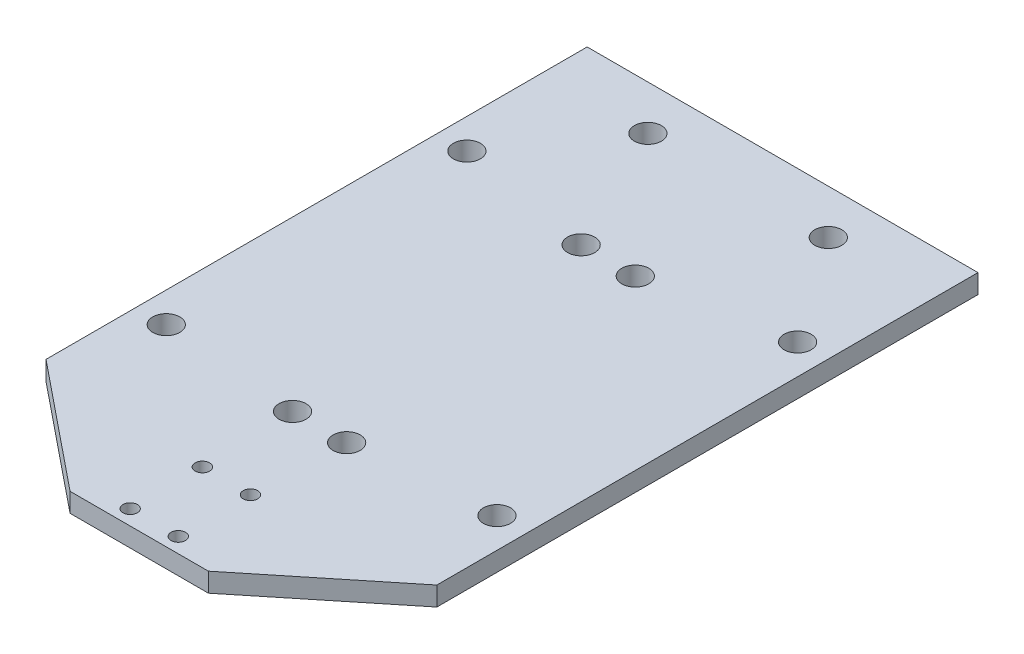
SolidWorks part; units mm, degrees
material "6061-T6 (SS)"
ref_plane "Front Plane" through (0, 0, 0) normal (0, 0, 1) x (1, 0, 0)
ref_plane "Top Plane" through (0, 0, 0) normal (0, 1, 0) x (1, 0, 0)
ref_plane "Right Plane" through (0, 0, 0) normal (1, 0, 0) x (0, 0, -1)
sketch "Sketch1" plane through (0, 0, 0) normal (0, 1, 0) x (1, 0, 0)
  line L0 (-11.5, -62) -> (-32.5, -45)
  line L1 (32.5, -45) -> (-32.5, -45)
  line L2 (32.5, -45) -> (32.5, 45)
  line L3 (32.5, 45) -> (-32.5, 45)
  line L4 (-32.5, -45) -> (-32.5, 45)
  line L5 (32.5, -45) -> (-32.5, 45) construction
  line L6 (32.5, 45) -> (-32.5, -45) construction
  line L7 (-11.5, -45) -> (11.5, -45)
  line L8 (-11.5, -45) -> (-11.5, -62)
  line L9 (-11.5, -62) -> (11.5, -62)
  line L10 (11.5, -45) -> (11.5, -62)
  line L11 (11.5, -62) -> (32.5, -45)
  line L12 (-32.5, -45) -> (32.5, -45)
  line L13 (11.5, -62) -> (-11.5, -62)
  point P0 (0, 0)
  point P10 (0, -62)
  dimension "D1" = 90
  dimension "D2" = 65
  dimension "D3" = 23
  dimension "D4" = 17
  dimension "D5" = 32.5
extrude "Boss-Extrude1" add sketch "Sketch1" along normal mid plane 3.175 contours L8 L1 L0 | L10 L11 L1 | L4 L1 L2 L3 | L10 L1 L8 L9
sketch "Sketch4" plane through (0, 1.5875, 0) normal (0, 1, 0) x (1, 0, 0)
  line L0 (-11.5, -62) -> (11.5, -62) construction
  point P0 (-4, -59.5)
  point P2 (4, -59.5)
  point P4 (4, -47.5)
  point P6 (-4, -47.5)
  point P16 (0, -62)
  dimension "D1" = 8
  dimension "D2" = 12
  dimension "D3" = 4
  dimension "D4" = 2.5
hole_wizard "M2 Clearance Hole1" positions "Sketch4" profile "Sketch3" hole size "M2" standard "ANSI Metric"
sketch "Sketch3" plane through (-4, 1.5875, 59.5) normal (1, 0, 0) x (0, 0, 1)
  line L0 (0, 0) -> (0, 3.175)
  line L1 (0, 3.175) -> (1.2, 3.175)
  line L2 (1.2, 3.175) -> (1.2, 0)
  line L5 (1.2, 0) -> (0, 0)
  line L11 (0, -6.35) -> (0, 107.95) construction
  dimension "Thru Hole Dia." = 2.4
  dimension "Thru Hole Depth" = 3.175
sketch "Sketch7" plane through (0, 1.5875, 0) normal (0, 1, 0) x (1, 0, 0)
  line L0 (-32.5, -45) -> (-32.5, 45) construction
  line L1 (32.5, -45) -> (32.5, 45) construction
  line L2 (32.5, 45) -> (-32.5, 45) construction
  point P0 (-27.5, 20)
  point P2 (27.5, 20)
  point P4 (27.5, -30)
  point P6 (-27.5, -30)
  dimension "D1" = 5
  dimension "D2" = 5
  dimension "D3" = 25
  dimension "D4" = 50
hole_wizard "M4 Clearance Hole1" positions "Sketch7" profile "Sketch6" hole size "M4" standard "ANSI Metric"
sketch "Sketch6" plane through (-27.5, 1.5875, -20) normal (1, 0, 0) x (0, 0, 1)
  line L0 (0, 0) -> (0, 3.175)
  line L1 (0, 3.175) -> (2.25, 3.175)
  line L2 (2.25, 3.175) -> (2.25, 0)
  line L5 (2.25, 0) -> (0, 0)
  line L11 (0, -6.35) -> (0, 107.95) construction
  dimension "Thru Hole Dia." = 4.5
  dimension "Thru Hole Depth" = 3.175
hole_wizard "M4 Clearance Hole2" positions "Sketch12" profile "Sketch9" hole size "M4" standard "ANSI Metric"
sketch "Sketch12" plane through (0, 1.5875, 0) normal (0, 1, 0) x (1, 0, 0)
  line L0 (-11.5, -62) -> (11.5, -62) construction
  point P0 (-4.5, -32)
  point P2 (4.5, -32)
  point P4 (4.5, 16)
  point P6 (-4.5, 16)
  point P17 (0, -62)
  dimension "D1" = 48
  dimension "D2" = 9
  dimension "D3" = 4.5
  dimension "D4" = 30
sketch "Sketch9" plane through (-4.5, 1.5875, 32) normal (1, 0, 0) x (0, 0, 1)
  line L0 (0, 0) -> (0, 3.175)
  line L1 (0, 3.175) -> (2.25, 3.175)
  line L2 (2.25, 3.175) -> (2.25, 0)
  line L5 (2.25, 0) -> (0, 0)
  line L11 (0, -6.35) -> (0, 107.95) construction
  dimension "Thru Hole Dia." = 4.5
  dimension "Thru Hole Depth" = 3.175
hole_wizard "M4 Clearance Hole3" positions "Sketch15" profile "Sketch14" hole size "M4" standard "ANSI Metric" end condition through all
sketch "Sketch15" plane through (0, 1.5875, 0) normal (0, 1, 0) x (1, 0, 0)
  point P0 (15, 37.6)
  point P3 (-15, 37.6)
sketch "Sketch14" plane through (15, 1.5875, -37.6) normal (1, 0, 0) x (0, 0, 1)
  line L0 (0, 0) -> (0, 3.175)
  line L1 (0, 3.175) -> (2.25, 3.175)
  line L2 (2.25, 3.175) -> (2.25, 0)
  line L5 (2.25, 0) -> (0, 0)
  line L11 (0, -6.35) -> (0, 107.95) construction
  dimension "Thru Hole Dia." = 4.5
  dimension "Thru Hole Depth" = 3.175
